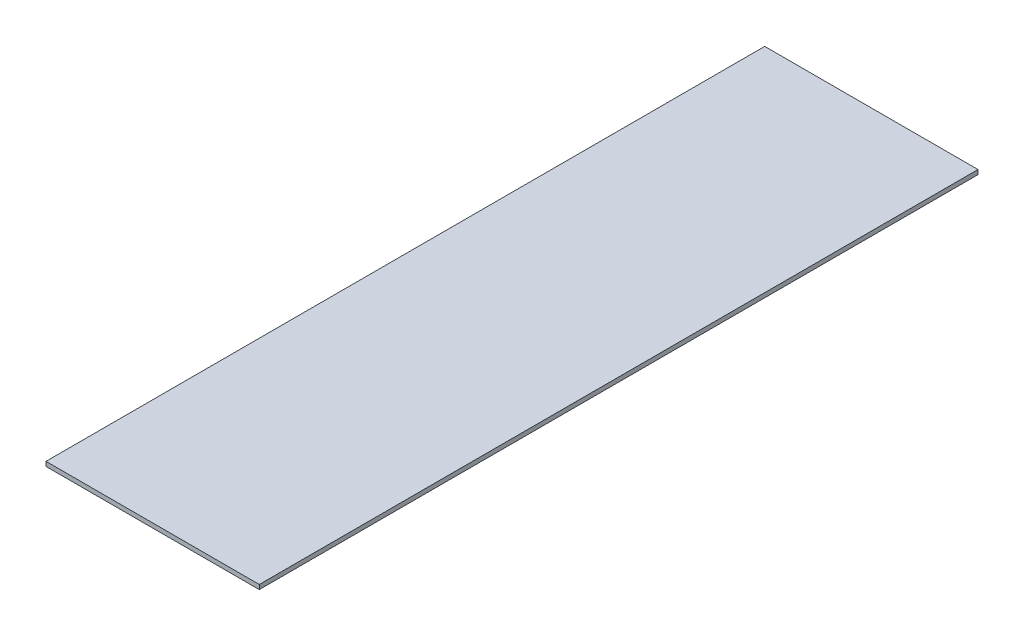
SolidWorks part; units mm, degrees
ref_plane "Front Plane" through (0, 0, 0) normal (0, 0, 1) x (1, 0, 0)
ref_plane "Top Plane" through (0, 0, 0) normal (0, 1, 0) x (1, 0, 0)
ref_plane "Right Plane" through (0, 0, 0) normal (1, 0, 0) x (0, 0, -1)
sketch "Sketch1" plane through (0, 0, 0) normal (0, 1, 0) x (1, 0, 0)
  line L0 (2, 325.5) -> (98, 325.5)
  line L1 (0, 0) -> (100, 0)
  line L2 (0, 0) -> (0, 327.5)
  line L3 (0, 327.5) -> (100, 327.5)
  line L4 (100, 0) -> (100, 327.5)
  line L5 (98, 2) -> (98, 325.5)
  line L6 (2, 2) -> (98, 2)
  line L7 (2, 2) -> (2, 325.5)
  dimension "D1" = 327.5
  dimension "D2" = 100
  dimension "D3" = 2
extrude "Boss-Extrude1" add sketch "Sketch1" along normal blind 2 contours L0 L5 L6 L7
